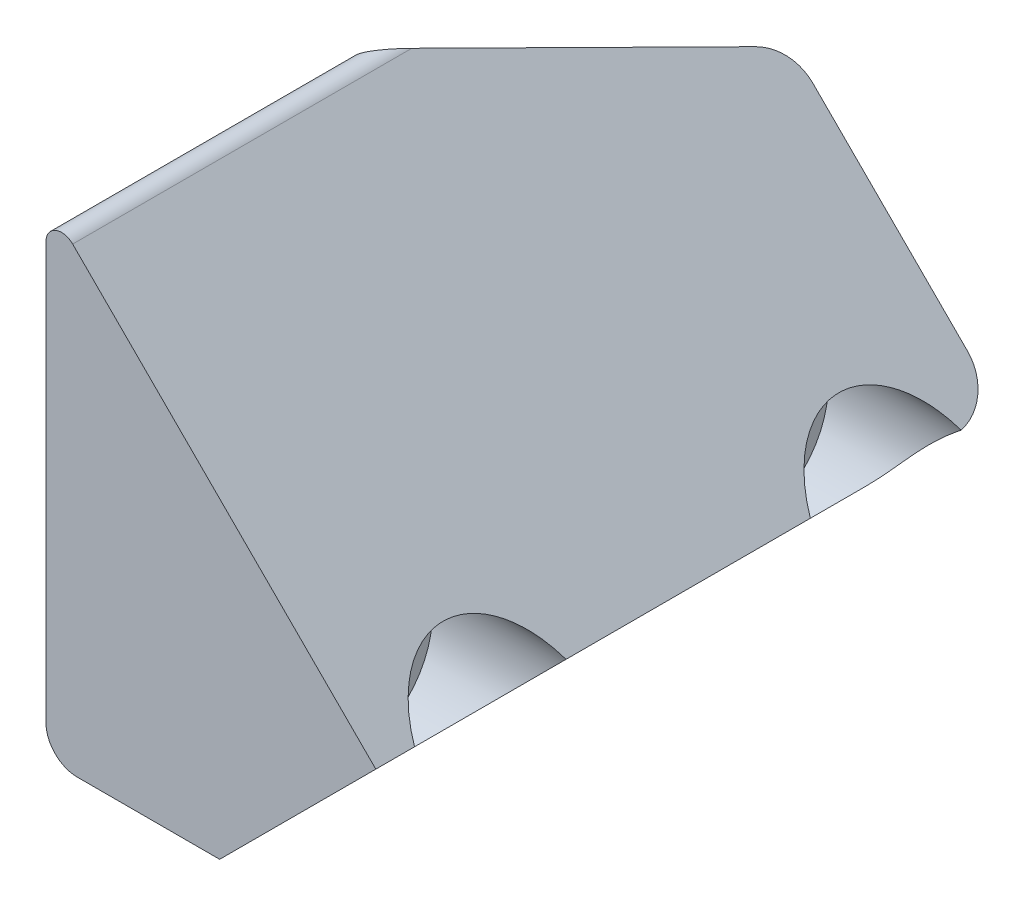
SolidWorks part; units mm, degrees
ref_plane "Front Plane" through (0, 0, 0) normal (0, 0, 1) x (1, 0, 0)
ref_plane "Top Plane" through (0, 0, 0) normal (0, 1, 0) x (1, 0, 0)
ref_plane "Right Plane" through (0, 0, 0) normal (1, 0, 0) x (0, 0, -1)
sketch "Sketch1" plane through (0, 0, 0) normal (0, 0, 1) x (1, 0, 0)
  line L0 (0, 0) -> (0, 15.5563)
  line L1 (0, 15.5563) -> (15.5563, 0)
  line L2 (15.5563, 0) -> (0, 0)
  dimension "D1" = 22
extrude "Boss-Extrude1" add sketch "Sketch1" along normal blind 20
sketch "Sketch2" plane through (7.7782, 7.7782, 0) normal (0.7071, 0.7071, 0) x (0, 0, -1)
  line L0 (-3.2904, -5.8042) -> (-3.2904, 8.4338) construction
  line L1 (-16.7096, 6.9519) -> (-16.7096, -5.8042) construction
  line L2 (-20, 11) -> (0, 11) construction
  line L3 (-9.7437, 2.4565) -> (-12.7002, 2.4565) construction
  line L4 (-9.7437, 2.4565) -> (-9.7437, -2.021) construction
  line L8 (-10, -8.5182) -> (-10, -5.8042) construction
  line L9 (-10, -5.8042) -> (-3.2904, -5.8042) construction
  line L10 (-10, -5.8042) -> (-16.7096, -5.8042) construction
  line L11 (-20, -11) -> (-20, 11) construction
  line L12 (0, -11) -> (0, 11) construction
  spline S1 degree 3 poles (-14.1004, 0.9749) (-14.6372, 2.0693) (-15.1036, 3.1324) (-15.5314, 4.2331) (-15.9115, 5.1606) (-16.2794, 5.9077) (-16.5299, 6.4545) (-16.6285, 6.9805) (-16.4423, 7.7153) (-15.8039, 8.5017) (-14.6332, 8.5781) (-13.5666, 8.0672) (-12.4675, 7.5689) (-11.3455, 7.1755) (-10.2494, 6.7115) (-8.7893, 6.0796) (-6.9166, 5.4214) (-5.0728, 4.6512) (-3.9366, 3.581) (-3.4049, 2.4964) (-3.3742, 1.342) (-3.7942, 0.2153) (-4.4561, -0.7358) (-5.3712, -1.5188) (-6.4471, -1.857) (-7.6593, -1.8728) (-8.8676, -1.9308) (-10.0498, -2.119) (-11.2149, -2.2469) (-12.3717, -1.9956) (-13.2394, -1.2341) (-13.7489, -0.154) (-14.1004, 0.9749) (-14.6372, 2.0693) (-15.1036, 3.1324) knots -0.09375 -0.0625 -0.03125 0 0.03125 0.0625 0.09375 0.109375 0.125 0.140625 0.15625 0.1875 0.21875 0.25 0.28125 0.3125 0.34375 0.375 0.4375 0.5 0.53125 0.5625 0.59375 0.625 0.65625 0.6875 0.71875 0.75 0.78125 0.8125 0.84375 0.875 0.90625 0.9375 0.96875 1 1.03125 1.0625 1.09375 only from (-14.6255, 2.0641) to (-14.6255, 2.0641)
  point P2 (-9.7437, 2.4565)
  dimension "D9" = 6.4533
  dimension "D24" = 6.966
  dimension "D30" = 4.4954
sketch "Sketch6" plane through (0, 0, 0) normal (-1, 0, 0) x (0, 0, 1)
  circle A2 centre (16.335, 3.8116) radius 1.6
  circle A3 centre (3.665, 3.8116) radius 1.6
  dimension "D1" = 3.2
extrude "Cut-Extrude4" cut sketch "Sketch6" against normal through all
ref_plane "Plane2" through (6, 0, 0) normal (-1, 0, 0) x (0, 0, 1)
sketch "Sketch7" plane through (6, 0, 0) normal (-1, 0, 0) x (0, 0, 1)
  circle A0 centre (16.335, 3.8116) radius 2.7
  circle A1 centre (3.665, 3.8116) radius 2.7
  dimension "D1" = 5.4
extrude "Cut-Extrude5" cut sketch "Sketch7" against normal through all
fillet "Fillet4" radius 1 1 edges at (0, 0, 10)
fillet "Fillet5" radius 0.5 2 edges at (15.5563, 0, 10) (0, 15.5563, 10)
sketch "Sketch8" plane through (7.7782, 7.7782, 0) normal (0.7071, 0.7071, 0) x (0, 0, -1)
  line L1 (-20, -12.3331) -> (0, -12.3331)
  line L3 (0, -12.3331) -> (0.0122, -3.9306)
  line L5 (-20, -3.9306) -> (-20, -12.3331)
  line L6 (-20, -3.9306) -> (0.0122, -3.9306)
  line L7 (-20, -9.7929) -> (0, -9.7929) construction
extrude "Cut-Extrude6" cut sketch "Sketch8" against normal blind 10
sketch "Sketch9" plane through (7.7782, 7.7782, 0) normal (0.7071, 0.7071, 0) x (0, 0, -1)
  line L0 (-11.3232, 10.8088) -> (0, 5.5287)
  line L2 (0, -3.9306) -> (0, 9.7929) construction
  line L4 (0, 5.5287) -> (0, 10.8088)
  line L5 (0, 10.8088) -> (-11.3232, 10.8088)
extrude "Cut-Extrude7" cut sketch "Sketch9" against normal blind 10
fillet "Fillet6" radius 1.5 2 edges at (8.0581, 2.4994, 0) (1.9344, 9.7531, 0)
